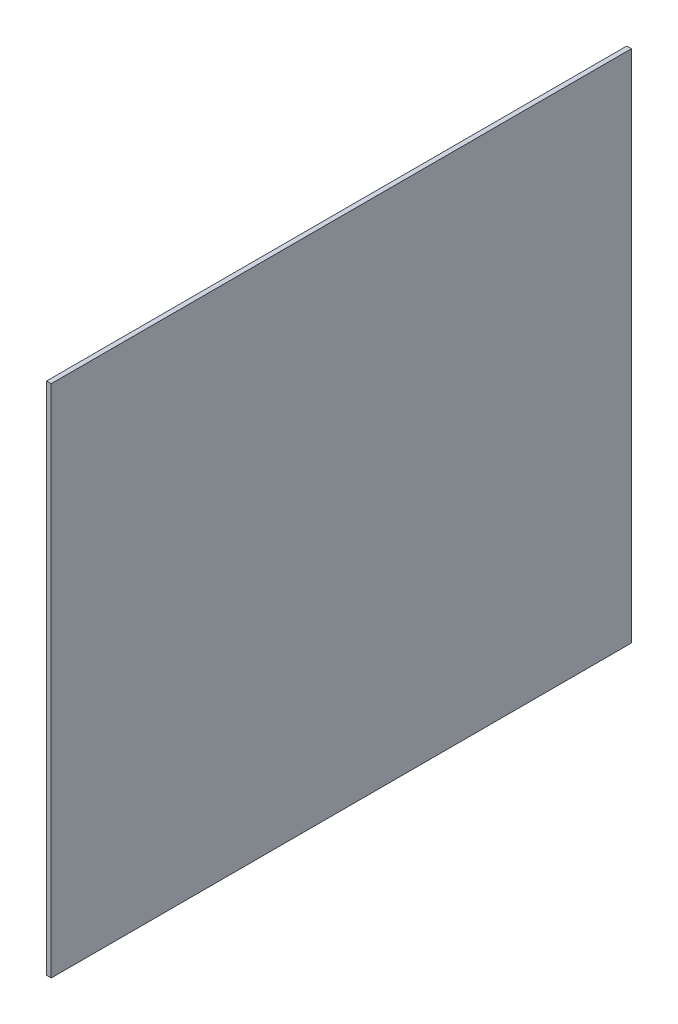
SolidWorks part; units mm, degrees
ref_plane "Front Plane" through (0, 0, 0) normal (0, 0, 1) x (1, 0, 0)
ref_plane "Top Plane" through (0, 0, 0) normal (0, 1, 0) x (1, 0, 0)
ref_plane "Right Plane" through (0, 0, 0) normal (1, 0, 0) x (0, 0, -1)
sketch "Croquis1" plane through (0, 0, 0) normal (1, 0, 0) x (0, 0, -1)
  line L1 (0, 0) -> (12.4, 0)
  line L2 (0, 0) -> (0, 11)
  line L3 (0, 11) -> (12.4, 11)
  line L4 (12.4, 0) -> (12.4, 11)
  dimension "D1" = 12.4
  dimension "D2" = 11
extrude "Saliente-Extruir1" add sketch "Croquis1" along normal blind 0.1
sketch "Croquis2"
